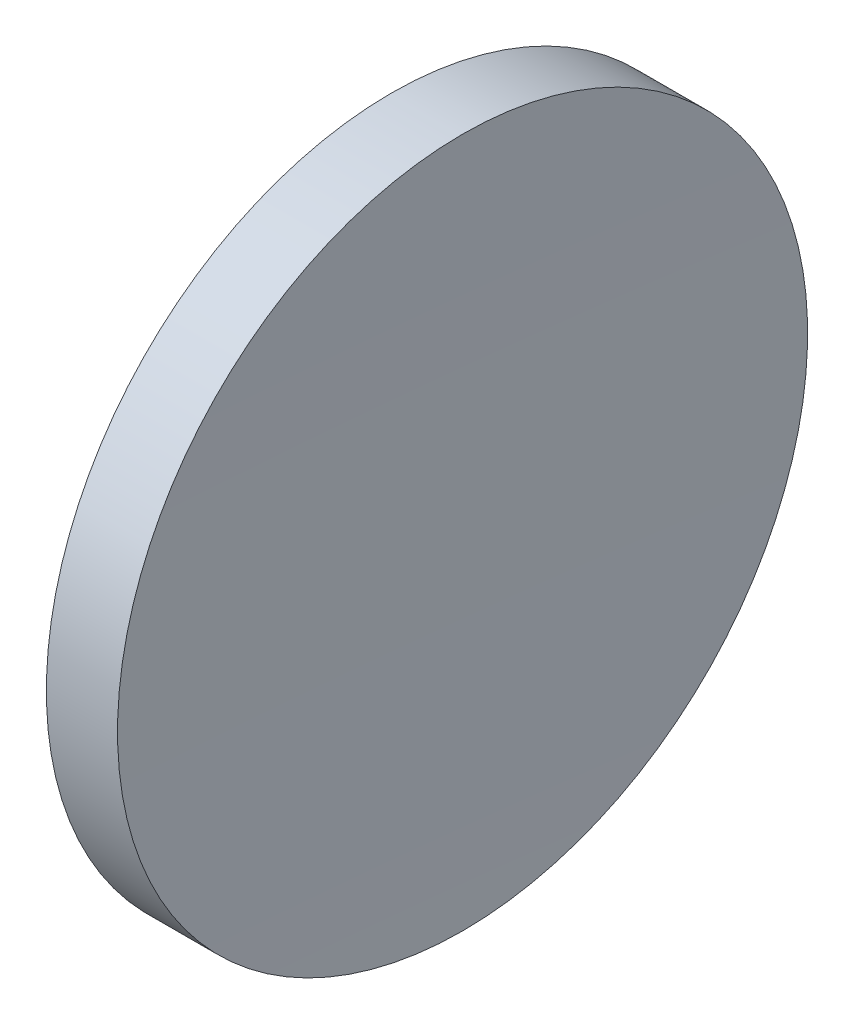
SolidWorks part; units mm, degrees
ref_plane "前视基准面" through (0, 0, 0) normal (0, 0, 1) x (1, 0, 0)
ref_plane "上视基准面" through (0, 0, 0) normal (0, 1, 0) x (1, 0, 0)
ref_plane "右视基准面" through (0, 0, 0) normal (1, 0, 0) x (0, 0, -1)
sketch "草图1" plane through (0, 0, 0) normal (0, 0, 1) x (1, 0, 0)
  line L0 (115.9445, 65.2168) -> (135.9482, 65.2168) construction
  line L1 (122.9597, 77.7168) -> (125.538, 77.7168)
  line L2 (122.6122, 65.2168) -> (125.4122, 65.2168)
  arc A0 (122.9597, 77.7168) -> (122.6122, 65.2168) centre (347.6122, 65.2168) ccw
  arc A1 (125.538, 77.7168) -> (125.4122, 65.2168) centre (746.4122, 65.2168) ccw
revolve "旋转1" add sketch "草图1" angle 360 about L0
